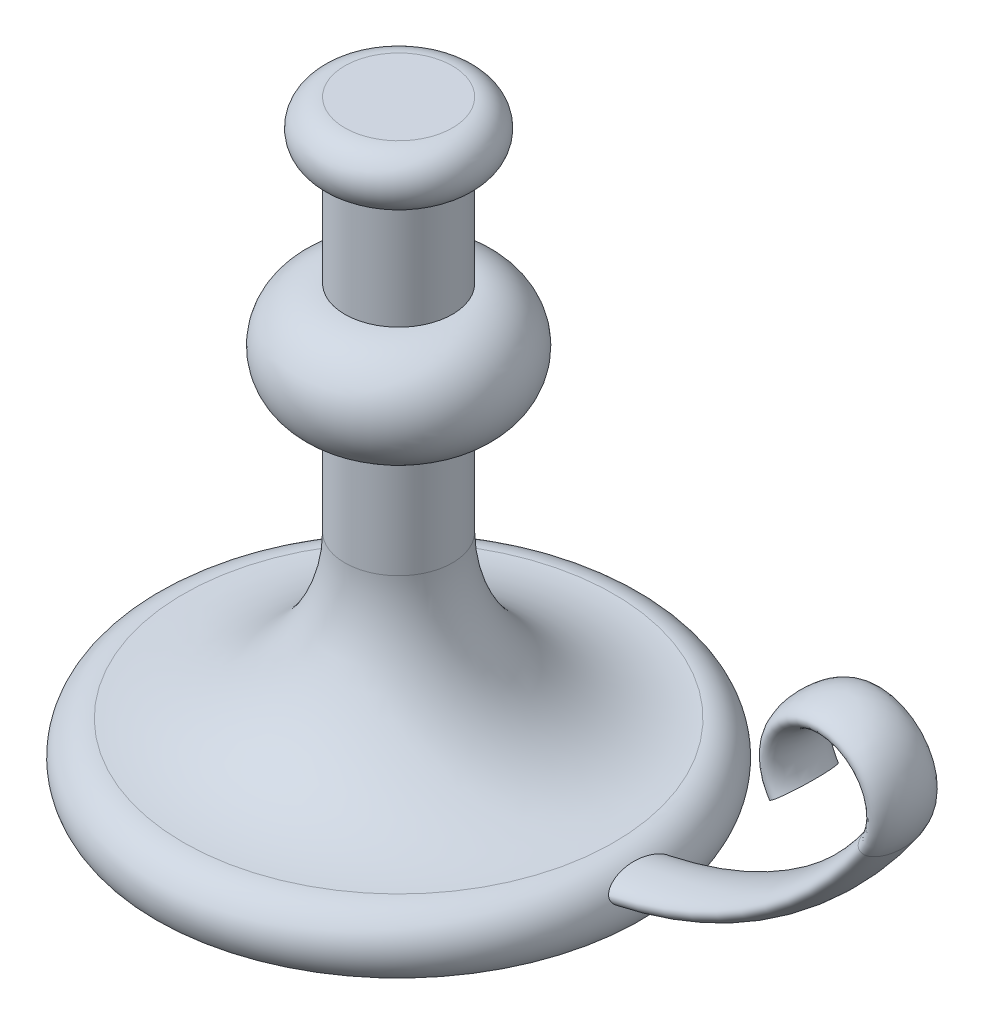
SolidWorks part; units mm, degrees
ref_plane "Front" through (0, 0, 0) normal (0, 0, 1) x (1, 0, 0)
ref_plane "Top" through (0, 0, 0) normal (0, 1, 0) x (1, 0, 0)
ref_plane "Right" through (0, 0, 0) normal (1, 0, 0) x (0, 0, -1)
other "Configuration Table"
sketch "Sketch1" plane through (0, 0, 0) normal (0, 0, 1) x (1, 0, 0)
  line L0 (0, 0) -> (0, 220)
  line L1 (0, 0) -> (90, 0)
  line L2 (0, 220) -> (20, 220)
  line L3 (20, 200) -> (20, 160)
  line L4 (20, 120) -> (20, 80)
  line L5 (0, 301.6619) -> (0, -95.609) construction
  arc A0 (20, 220) -> (20, 200) centre (20, 210) cw
  arc A1 (20, 160) -> (20, 120) centre (20, 140) cw
  arc A2 (20, 80) -> (80, 20) centre (80, 80) ccw
  arc A3 (80, 20) -> (90, 0) centre (80, 7.5) cw
  dimension "D4" = 40
  dimension "D5" = 20
  dimension "D7" = 10
  dimension "D10" = 12.5
  dimension "D8" = 20
  dimension "D9" = 60
  dimension "D1" = 220
  dimension "D2" = 90
  dimension "D3" = 20
  dimension "D6" = 80
revolve "Revolve1" add sketch "Sketch1" angle 360 about L5
sketch "Sketch2" plane through (0, 0, 0) normal (0, 0, 1) x (1, 0, 0)
  line L0 (0, 10) -> (60, 10)
  line L1 (0, 301.6619) -> (0, -95.609) construction
  arc A0 (60, 10) -> (183.5921, 75) centre (60, 160) ccw
  arc A1 (183.5921, 75) -> (150.6342, 75) centre (167.1131, 86.3333) ccw
  dimension "D1" = 65
  dimension "D2" = 150
  dimension "D3" = 20
  dimension "D4" = 10
  dimension "D5" = 60
sketch "Sketch3" plane through (0, 0, 0) normal (1, 0, 0) x (0, 0, -1)
  ellipse E0 centre (0, 10) end of major axis (12.108, 10) minor radius 5
  dimension "D1" = 10
sweep "Sweep1" add profiles "Sketch3" path "Sketch2"
